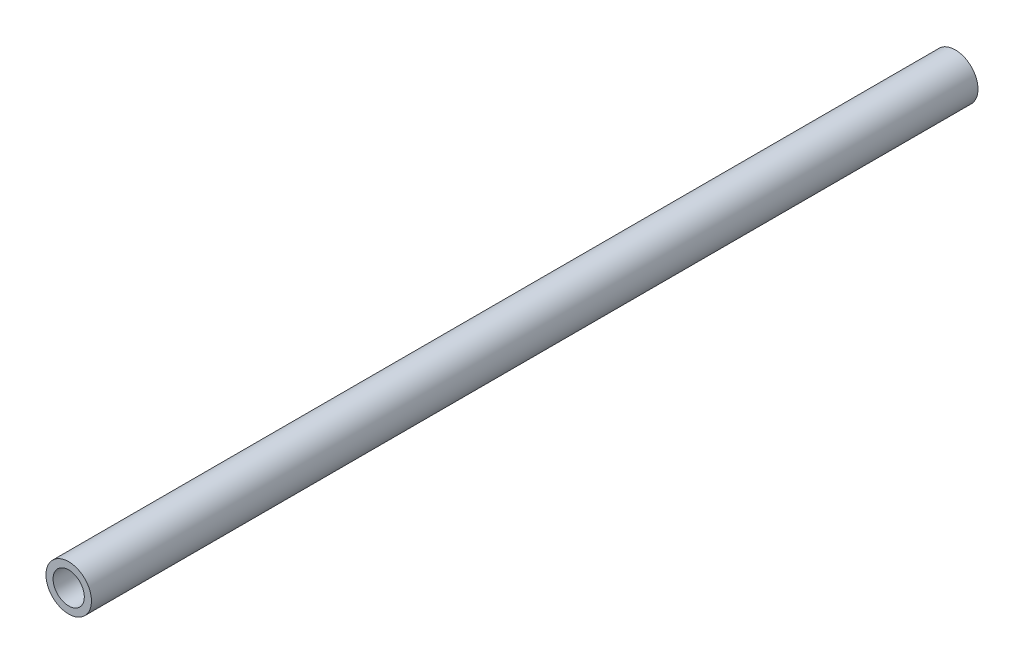
SolidWorks part; units mm, degrees
material "Cast Carbon Steel"
ref_plane "Front Plane" through (0, 0, 0) normal (0, 0, 1) x (1, 0, 0)
ref_plane "Top Plane" through (0, 0, 0) normal (0, 1, 0) x (1, 0, 0)
ref_plane "Right Plane" through (0, 0, 0) normal (1, 0, 0) x (0, 0, -1)
sketch "Sketch1" plane through (0, 0, 0) normal (0, 0, 1) x (1, 0, 0)
  circle A0 centre (0, 0) radius 12.7
  circle A1 centre (0, 0) radius 8.7312
  point P5 (0, 0)
  dimension "D1" = 25.4
  dimension "D2" = 17.4625
extrude "Boss-Extrude1" add sketch "Sketch1" along normal blind 495.3
